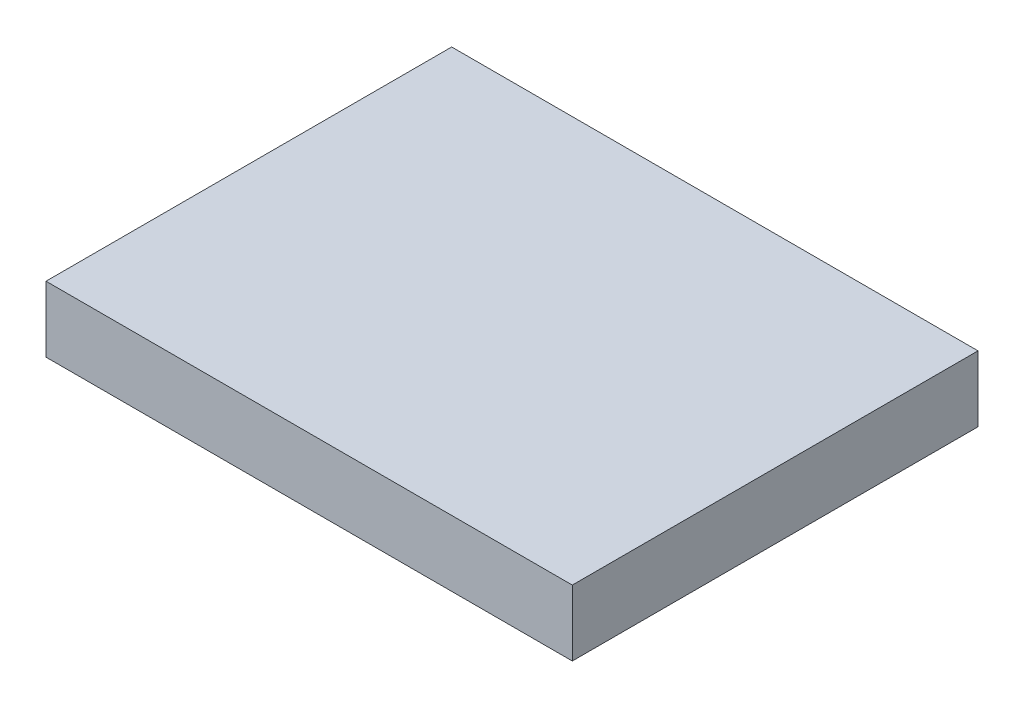
SolidWorks part; units mm, degrees
material "Polyurethane Foam Flexible"
ref_plane "Front Plane" through (0, 0, 0) normal (0, 0, 1) x (1, 0, 0)
ref_plane "Top Plane" through (0, 0, 0) normal (0, 1, 0) x (1, 0, 0)
ref_plane "Right Plane" through (0, 0, 0) normal (1, 0, 0) x (0, 0, -1)
sketch "Sketch1" plane through (0, 0, 0) normal (0, 1, 0) x (1, 0, 0)
  line L1 (-120, -92.5) -> (120, -92.5)
  line L2 (-120, -92.5) -> (-120, 92.5)
  line L3 (-120, 92.5) -> (120, 92.5)
  line L4 (120, -92.5) -> (120, 92.5)
  line L5 (-120, -92.5) -> (120, 92.5) construction
  line L6 (-120, 92.5) -> (120, -92.5) construction
  point P0 (0, 0)
  dimension "D1" = 240
  dimension "D2" = 185
extrude "Boss-Extrude1" add sketch "Sketch1" along normal blind 30
